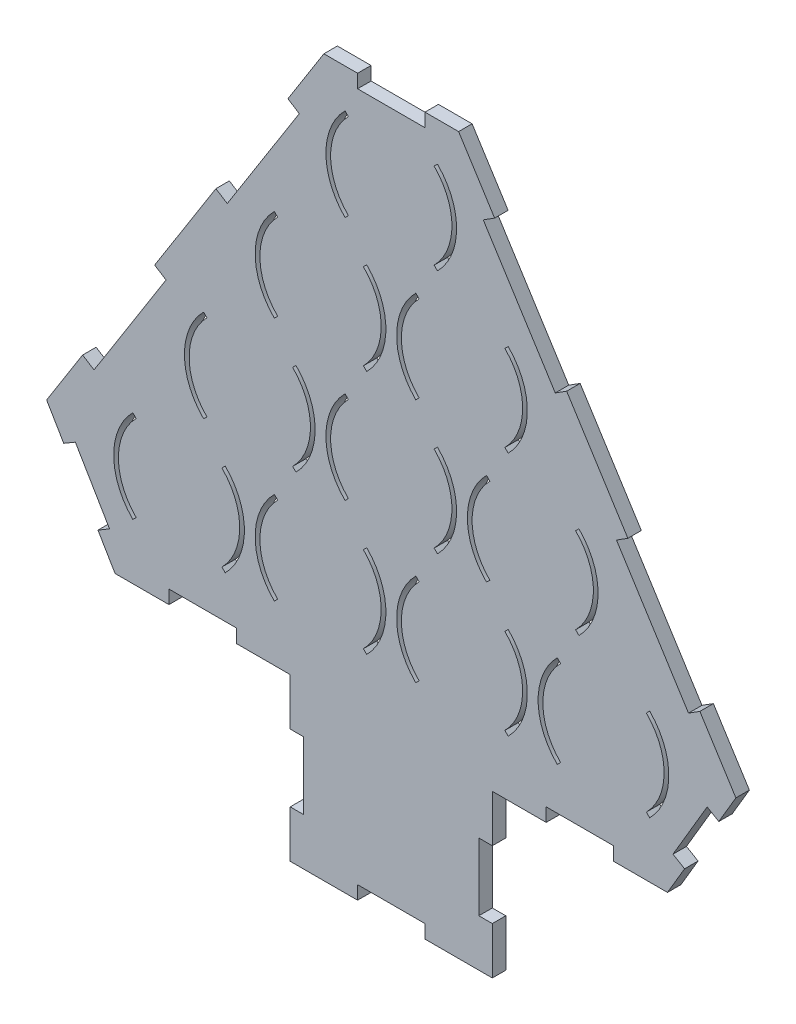
SolidWorks part; units mm, degrees
ref_plane "Plan de face" through (0, 0, 0) normal (0, 0, 1) x (1, 0, 0)
ref_plane "Plan de dessus" through (0, 0, 0) normal (0, 1, 0) x (1, 0, 0)
ref_plane "Plan de droite" through (0, 0, 0) normal (1, 0, 0) x (0, 0, -1)
sketch "Esquisse1" plane through (0, 0, 0) normal (0, 0, 1) x (1, 0, 0)
  line L0 (0, 0) -> (-371.1464, 0) construction
  line L1 (0, 0) -> (478.5179, 0) construction
  line L2 (0, 0) -> (0, 90.9327) construction
  line L3 (0, 90.9327) -> (-157.5, 90.9327) construction
  line L4 (0, 90.9327) -> (157.5, 90.9327) construction
  line L5 (0, 90.9327) -> (0, 181.8653) construction
  line L6 (0, 181.8653) -> (-52.5, 181.8653) construction
  line L7 (0, 181.8653) -> (52.5, 181.8653) construction
  line L8 (0, 181.8653) -> (0, 363.4062) construction
  line L12 (-157.5, 0) -> (-189.3198, -31.8198) construction
  line L13 (-157.5, 0) -> (-189.3198, 31.8198) construction
  line L14 (-189.3198, 31.8198) -> (-191.7947, 34.2947)
  line L15 (-189.3198, -31.8198) -> (-191.7947, -34.2947)
  line L16 (-157.5, 0) -> (-157.5, 43.1504) construction
  line L17 (-125.6802, 31.8198) -> (-123.2053, 34.2947)
  line L18 (-125.6802, -31.8198) -> (-123.2053, -34.2947)
  line L19 (-84.3198, -31.8198) -> (-86.7947, -34.2947)
  line L20 (-84.3198, 31.8198) -> (-86.7947, 34.2947)
  line L21 (-20.6802, 31.8198) -> (-18.2053, 34.2947)
  line L22 (-20.6802, -31.8198) -> (-18.2053, -34.2947)
  line L23 (20.6802, -31.8198) -> (18.2053, -34.2947)
  line L24 (20.6802, 31.8198) -> (18.2053, 34.2947)
  line L25 (84.3198, 31.8198) -> (86.7947, 34.2947)
  line L26 (84.3198, -31.8198) -> (86.7947, -34.2947)
  line L27 (125.6802, -31.8198) -> (123.2053, -34.2947)
  line L28 (125.6802, 31.8198) -> (123.2053, 34.2947)
  line L29 (189.3198, 31.8198) -> (191.7947, 34.2947)
  line L30 (189.3198, -31.8198) -> (191.7947, -34.2947)
  line L31 (-105, 90.9327) -> (-136.8198, 122.7525) construction
  line L32 (-105, 90.9327) -> (-136.8198, 59.1129) construction
  line L33 (-139.2947, 56.638) -> (-136.8198, 59.1129)
  line L34 (-136.8198, 122.7525) -> (-139.2947, 125.2273)
  line L35 (-105, 90.9327) -> (-105, 127.4436) construction
  line L36 (-70.7053, 56.638) -> (-73.1802, 59.1129)
  line L37 (-73.1802, 122.7525) -> (-70.7053, 125.2273)
  line L38 (-31.8198, 122.7525) -> (-34.2947, 125.2273)
  line L39 (-34.2947, 56.638) -> (-31.8198, 59.1129)
  line L40 (34.2947, 56.638) -> (31.8198, 59.1129)
  line L41 (31.8198, 122.7525) -> (34.2947, 125.2273)
  line L42 (73.1802, 122.7525) -> (70.7053, 125.2273)
  line L43 (70.7053, 56.638) -> (73.1802, 59.1129)
  line L44 (139.2947, 56.638) -> (136.8198, 59.1129)
  line L45 (136.8198, 122.7525) -> (139.2947, 125.2273)
  line L46 (-52.5, 181.8653) -> (-86.7947, 216.16) construction
  line L47 (-52.5, 181.8653) -> (-86.7947, 147.5707) construction
  line L48 (-52.5, 181.8653) -> (-100, 181.8653) construction
  line L49 (-84.3198, 213.6851) -> (-86.7947, 216.16)
  line L50 (-84.3198, 150.0455) -> (-86.7947, 147.5707)
  line L51 (-52.5, 181.8653) -> (-52.5, 219.5882) construction
  line L52 (-20.6802, 213.6851) -> (-18.2053, 216.16)
  line L53 (-20.6802, 150.0455) -> (-18.2053, 147.5707)
  line L54 (20.6802, 150.0455) -> (18.2053, 147.5707)
  line L55 (20.6802, 213.6851) -> (18.2053, 216.16)
  line L56 (84.3198, 150.0455) -> (86.7947, 147.5707)
  line L57 (84.3198, 213.6851) -> (86.7947, 216.16)
  line L58 (0, 272.798) -> (-34.2947, 307.0927) construction
  line L59 (0, 272.798) -> (-47.5, 272.798) construction
  line L60 (0, 272.798) -> (-34.2947, 238.5033) construction
  line L61 (-31.8198, 304.6178) -> (-34.2947, 307.0927)
  line L62 (-31.8198, 240.9782) -> (-34.2947, 238.5033)
  line L63 (31.8198, 304.6178) -> (34.2947, 307.0927)
  line L64 (31.8198, 240.9782) -> (34.2947, 238.5033)
  line L65 (-50, 335.9011) -> (50, 335.9011)
  line L66 (-255.7759, 10.5071) -> (-205, -75.6429)
  line L67 (255.7759, 10.5071) -> (205, -75.6429)
  line L68 (-205, -75.6429) -> (205, -75.6429)
  line L69 (-50, 335.9011) -> (-255.7759, 10.5071)
  line L70 (50, 335.9011) -> (255.7759, 10.5071)
  line L71 (-50, 335.9011) -> (-50, -75.6429) construction
  line L72 (50, 335.9011) -> (50, -75.6429) construction
  arc A10 (-189.3198, -31.8198) -> (-189.3198, 31.8198) centre (-157.5, 0) cw
  arc A11 (-191.7947, -34.2947) -> (-191.7947, 34.2947) centre (-157.5, 0) cw
  arc A12 (-125.6802, -31.8198) -> (-125.6802, 31.8198) centre (-157.5, 0) ccw
  arc A13 (-123.2053, -34.2947) -> (-123.2053, 34.2947) centre (-157.5, 0) ccw
  arc A14 (-86.7947, -34.2947) -> (-86.7947, 34.2947) centre (-52.5, 0) cw
  arc A15 (-84.3198, -31.8198) -> (-84.3198, 31.8198) centre (-52.5, 0) cw
  arc A16 (-20.6802, -31.8198) -> (-20.6802, 31.8198) centre (-52.5, 0) ccw
  arc A17 (-18.2053, -34.2947) -> (-18.2053, 34.2947) centre (-52.5, 0) ccw
  arc A18 (18.2053, -34.2947) -> (18.2053, 34.2947) centre (52.5, 0) cw
  arc A19 (20.6802, -31.8198) -> (20.6802, 31.8198) centre (52.5, 0) cw
  arc A20 (84.3198, -31.8198) -> (84.3198, 31.8198) centre (52.5, 0) ccw
  arc A21 (86.7947, -34.2947) -> (86.7947, 34.2947) centre (52.5, 0) ccw
  arc A22 (123.2053, -34.2947) -> (123.2053, 34.2947) centre (157.5, 0) cw
  arc A23 (125.6802, -31.8198) -> (125.6802, 31.8198) centre (157.5, 0) cw
  arc A24 (189.3198, -31.8198) -> (189.3198, 31.8198) centre (157.5, 0) ccw
  arc A25 (191.7947, -34.2947) -> (191.7947, 34.2947) centre (157.5, 0) ccw
  arc A26 (-136.8198, 122.7525) -> (-136.8198, 59.1129) centre (-105, 90.9327) ccw
  arc A27 (-139.2947, 125.2273) -> (-139.2947, 56.638) centre (-105, 90.9327) ccw
  arc A28 (-73.1802, 122.7525) -> (-73.1802, 59.1129) centre (-105, 90.9327) cw
  arc A29 (-70.7053, 125.2273) -> (-70.7053, 56.638) centre (-105, 90.9327) cw
  arc A30 (-34.2947, 125.2273) -> (-34.2947, 56.638) centre (0, 90.9327) ccw
  arc A31 (-31.8198, 122.7525) -> (-31.8198, 59.1129) centre (0, 90.9327) ccw
  arc A32 (31.8198, 122.7525) -> (31.8198, 59.1129) centre (0, 90.9327) cw
  arc A33 (34.2947, 125.2273) -> (34.2947, 56.638) centre (0, 90.9327) cw
  arc A34 (70.7053, 125.2273) -> (70.7053, 56.638) centre (105, 90.9327) ccw
  arc A35 (73.1802, 122.7525) -> (73.1802, 59.1129) centre (105, 90.9327) ccw
  arc A36 (136.8198, 122.7525) -> (136.8198, 59.1129) centre (105, 90.9327) cw
  arc A37 (139.2947, 125.2273) -> (139.2947, 56.638) centre (105, 90.9327) cw
  arc A38 (-86.7947, 216.16) -> (-86.7947, 147.5707) centre (-52.5, 181.8653) ccw
  arc A39 (-84.3198, 213.6851) -> (-84.3198, 150.0455) centre (-52.5, 181.8653) ccw
  arc A40 (-20.6802, 213.6851) -> (-20.6802, 150.0455) centre (-52.5, 181.8653) cw
  arc A41 (-18.2053, 216.16) -> (-18.2053, 147.5707) centre (-52.5, 181.8653) cw
  arc A42 (18.2053, 216.16) -> (18.2053, 147.5707) centre (52.5, 181.8653) ccw
  arc A43 (20.6802, 213.6851) -> (20.6802, 150.0455) centre (52.5, 181.8653) ccw
  arc A44 (84.3198, 213.6851) -> (84.3198, 150.0455) centre (52.5, 181.8653) cw
  arc A45 (86.7947, 216.16) -> (86.7947, 147.5707) centre (52.5, 181.8653) cw
  arc A46 (-34.2947, 307.0927) -> (-34.2947, 238.5033) centre (0, 272.798) ccw
  arc A47 (-31.8198, 304.6178) -> (-31.8198, 240.9782) centre (0, 272.798) ccw
  arc A48 (31.8198, 304.6178) -> (31.8198, 240.9782) centre (0, 272.798) cw
  arc A49 (34.2947, 307.0927) -> (34.2947, 238.5033) centre (0, 272.798) cw
  point P7 (-105, 90.9327)
  point P32 (-157.5, 0)
  point P95 (0, 272.798)
  dimension "D4" = 4
  dimension "D5" = 45
  dimension "D6" = 45
  dimension "D7" = 45
  dimension "D8" = 48.5
  dimension "D9" = 3
  dimension "D10" = 45
  dimension "D11" = 45
  dimension "D12" = 45
  dimension "D13" = 48.5
  dimension "D14" = 45
  dimension "D15" = 2
  dimension "D16" = 45
  dimension "D17" = 45
  dimension "D18" = 48.5
  dimension "D19" = 45
  dimension "D20" = 100
  dimension "D21" = 410
  dimension "D27" = 45
  dimension "D30" = 48.5
  dimension "D22" = 385
  dimension "D23" = 385
  dimension "D24" = 32.309
  dimension "D25" = 32.309
  dimension "D26" = 205
  dimension "D28" = 45
  dimension "D29" = 45
  dimension "D31" = 100
  dimension "D32" = 100
extrude "Boss.-Extru.1" add sketch "Esquisse1" along normal blind 10
sketch "Esquisse2" plane through (0, 0, 10) normal (0, 0, 1) x (1, 0, 0)
  line L0 (-205, -75.6429) -> (205, -75.6429) construction
  line L1 (75, -75.6429) -> (-75, -75.6429)
  line L2 (75, -75.6429) -> (75, -195.6429)
  line L3 (75, -195.6429) -> (-75, -195.6429)
  line L4 (-75, -75.6429) -> (-75, -195.6429)
  dimension "D1" = 150
  dimension "D2" = 120
  dimension "D3" = 75
extrude "Boss.-Extru.2" add sketch "Esquisse2" against normal blind 10
sketch "Esquisse3" plane through (0, 0, 10) normal (0, 0, 1) x (1, 0, 0)
  line L0 (-75, -75.6429) -> (-75, -195.6429) construction
  line L1 (-75, -110.6429) -> (-65, -110.6429)
  line L2 (-75, -110.6429) -> (-75, -160.6429)
  line L3 (-75, -160.6429) -> (-65, -160.6429)
  line L4 (-65, -110.6429) -> (-65, -160.6429)
  line L5 (-75, -195.6429) -> (75, -195.6429) construction
  line L6 (-25, -195.6429) -> (25, -195.6429)
  line L7 (-25, -195.6429) -> (-25, -185.6429)
  line L8 (-25, -185.6429) -> (25, -185.6429)
  line L9 (25, -195.6429) -> (25, -185.6429)
  line L10 (75, -195.6429) -> (75, -75.6429) construction
  line L11 (75, -110.6429) -> (65, -110.6429)
  line L12 (75, -110.6429) -> (75, -160.6429)
  line L13 (75, -160.6429) -> (65, -160.6429)
  line L14 (65, -110.6429) -> (65, -160.6429)
  line L15 (-205, -75.6429) -> (-75, -75.6429) construction
  line L16 (75, -75.6429) -> (205, -75.6429) construction
  dimension "D1" = 50
  dimension "D2" = 50
  dimension "D3" = 50
  dimension "D4" = 10
  dimension "D5" = 10
  dimension "D6" = 10
  dimension "D7" = 35
  dimension "D8" = 35
  dimension "D9" = 50
extrude "Enlèv. mat.-Extru.1" cut sketch "Esquisse3" against normal blind 10
sketch "Esquisse4" plane through (0, 0, 10) normal (0, 0, 1) x (1, 0, 0)
  line L0 (-205, -75.6429) -> (-75, -75.6429) construction
  line L1 (-165, -75.6429) -> (-115, -75.6429)
  line L2 (-165, -75.6429) -> (-165, -65.6429)
  line L3 (-165, -65.6429) -> (-115, -65.6429)
  line L4 (-115, -75.6429) -> (-115, -65.6429)
  line L11 (-217.694, -54.1054) -> (-209.079, -49.0278)
  line L12 (-255.7759, 10.5071) -> (-205, -75.6429) construction
  line L13 (-209.079, -49.0278) -> (-234.4669, -5.9528)
  line L14 (-234.4669, -5.9528) -> (-243.0819, -11.0304)
  line L15 (-243.0819, -11.0304) -> (-217.694, -54.1054)
  line L16 (-229.0517, 52.766) -> (-220.5999, 47.4212)
  line L17 (-50, 335.9011) -> (-255.7759, 10.5071) construction
  line L18 (-220.5999, 47.4212) -> (-167.1517, 131.9392)
  line L19 (-167.1517, 131.9392) -> (-175.6034, 137.284)
  line L20 (-175.6034, 137.284) -> (-229.0517, 52.766)
  line L23 (-68.2723, 288.2973) -> (-76.7241, 293.6422)
  line L25 (-68.2723, 288.2973) -> (-121.7206, 203.7794)
  line L26 (-121.7206, 203.7794) -> (-130.1724, 209.1242)
  line L27 (-130.1724, 209.1242) -> (-76.7241, 293.6422)
  line L28 (50, 335.9011) -> (-50, 335.9011) construction
  line L29 (-25, 335.9011) -> (25, 335.9011)
  line L30 (-25, 335.9011) -> (-25, 325.9011)
  line L31 (-25, 325.9011) -> (25, 325.9011)
  line L32 (25, 335.9011) -> (25, 325.9011)
  line L33 (0, 335.9011) -> (0, -65.6429) construction
  line L34 (165, -65.6429) -> (115, -65.6429)
  line L35 (115, -75.6429) -> (115, -65.6429)
  line L36 (165, -75.6429) -> (115, -75.6429)
  line L37 (165, -75.6429) -> (165, -65.6429)
  line L38 (234.4669, -5.9528) -> (243.0819, -11.0304)
  line L39 (209.079, -49.0278) -> (234.4669, -5.9528)
  line L40 (217.694, -54.1054) -> (209.079, -49.0278)
  line L41 (243.0819, -11.0304) -> (217.694, -54.1054)
  line L42 (167.1517, 131.9392) -> (175.6034, 137.284)
  line L43 (220.5999, 47.4212) -> (167.1517, 131.9392)
  line L44 (229.0517, 52.766) -> (220.5999, 47.4212)
  line L45 (175.6034, 137.284) -> (229.0517, 52.766)
  line L46 (121.7206, 203.7794) -> (130.1724, 209.1242)
  line L47 (68.2723, 288.2973) -> (121.7206, 203.7794)
  line L48 (68.2723, 288.2973) -> (76.7241, 293.6422)
  line L49 (130.1724, 209.1242) -> (76.7241, 293.6422)
  dimension "D1" = 10
  dimension "D2" = 50
  dimension "D3" = 10
  dimension "D4" = 50
  dimension "D5" = 40
  dimension "D6" = 25
  dimension "D7" = 10
  dimension "D8" = 100
  dimension "D9" = 10
  dimension "D10" = 50
  dimension "D11" = 50
  dimension "D12" = 100
  dimension "D13" = 10
  dimension "D14" = 50
  dimension "D15" = 25
extrude "Enlèv. mat.-Extru.2" cut sketch "Esquisse4" against normal blind 10
